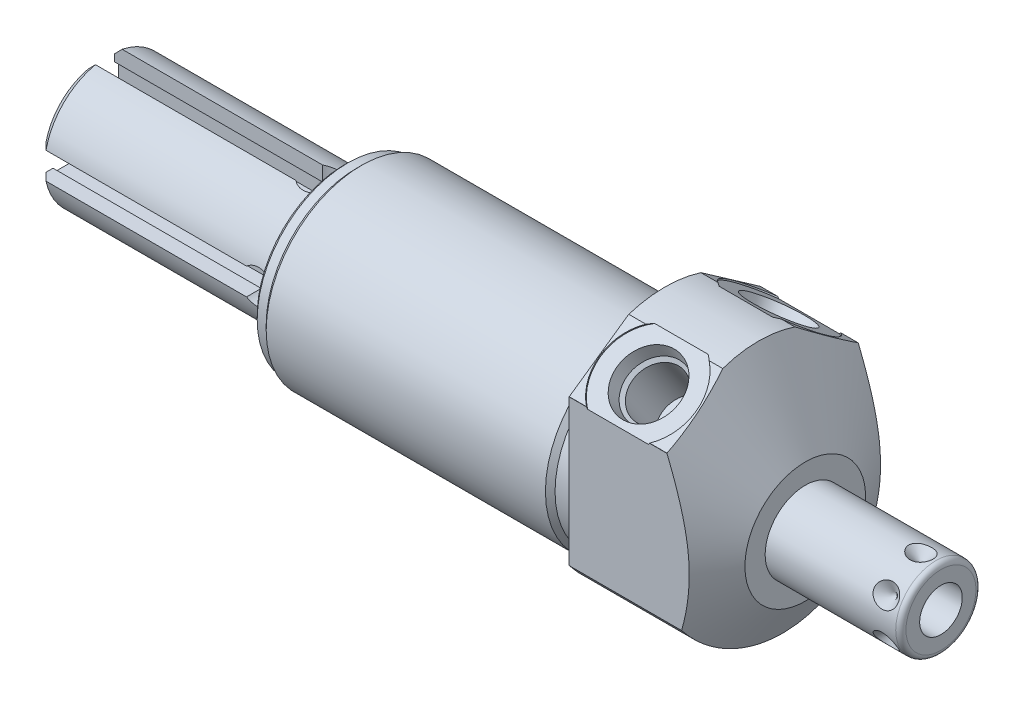
SolidWorks part; units mm, degrees
material "Alloy Steel"
ref_plane "Front Plane" through (0, 0, 0) normal (0, 0, 1) x (1, 0, 0)
ref_plane "Top Plane" through (0, 0, 0) normal (0, 1, 0) x (1, 0, 0)
ref_plane "Right Plane" through (0, 0, 0) normal (1, 0, 0) x (0, 0, -1)
ref_plane "Plane1" through (0, 0, 0) normal (1, 0, 0) x (0, 0, -1)
sketch "Sketch1" plane through (0, 0, 0) normal (1, 0, 0) x (0, 0, -1)
  circle A0 centre (0, 0) radius 23.8125
  dimension "D1" = 47.625
extrude "Extrude1" add sketch "Sketch1" along normal blind 27.7876 and the other way blind 63.5
ref_plane "Plane2" through (0, 0, 0) normal (1, 0, 0) x (0, 0, -1)
sketch "Sketch2" plane through (0, 0, 0) normal (1, 0, 0) x (0, 0, -1)
  line L0 (-20.7455, -4.191) -> (20.7455, -4.191) construction
  circle A0 centre (0, -4.191) radius 18.8595
  circle A1 centre (0, 0) radius 23.8125 construction
  circle A2 centre (0, 0) radius 23.8125
  dimension "D2" = 37.719
  dimension "D1" = 4.191
extrude "Cut-Extrude1" cut sketch "Sketch2" against normal up to next
ref_plane "Plane4" through (0, 0, 0) normal (-1, 0, 0) x (0, 0, 1)
sketch "Sketch4" plane through (0, 0, 0) normal (-1, 0, 0) x (0, 0, 1)
  line L0 (18.923, -14.4553) -> (18.923, 14.4659)
  line L1 (18.923, 14.4659) -> (0, 27.7159)
  line L2 (-18.923, -14.4553) -> (-18.923, 14.4659)
  line L3 (-18.923, 14.4659) -> (0, 27.7159)
  line L4 (0, -26.3889) -> (0, 30.2923) construction
  circle A0 centre (0, 0) radius 28.575
  circle A1 centre (0, 0) radius 23.8125 construction
  arc A3 (-18.923, -14.4553) -> (18.923, -14.4553) centre (0, 0) ccw
  dimension "D4" = 57.15
  dimension "D1" = 37.846
  dimension "D2" = 27.7159
  dimension "D3" = 55
extrude "Cut-Extrude3" cut sketch "Sketch4" against normal up to next
ref_plane "Plane6" through (0, 0, 0) normal (0, 0, 1) x (1, 0, 0)
sketch "Sketch6" plane through (0, 0, 0) normal (0, 0, 1) x (1, 0, 0)
  line L0 (4.764, 47.625) -> (27.7876, 7.747)
  line L1 (3.6128, -4.191) -> (28.9388, -4.191) construction
  line L2 (-63.5, -4.191) -> (0, -4.191) construction
  line L3 (27.7876, 7.747) -> (27.7876, 47.625)
  line L4 (27.7876, 47.625) -> (4.764, 47.625)
  line L5 (27.7876, -14.4553) -> (27.7876, 14.4553) construction
  dimension "D1" = 23.876
  dimension "D2" = 30
  dimension "D3" = 39.878
revolve "Cut-Revolve2" cut sketch "Sketch6" angle 360 about L1
ref_plane "Plane7" through (9.652, 18.3948, 12.869) normal (1, 0, 0) x (0, 0.5736, -0.8192)
sketch "S2D0002" plane through (9.652, 18.3948, 12.869) normal (1, 0, 0) x (0, 0.5736, -0.8192)
  line L0 (0, 0) -> (6.1849, 0)
  line L1 (6.1849, 0) -> (5.6423, -2.5527)
  line L2 (5.6423, -2.5527) -> (4.9784, -3.2166)
  line L3 (4.9784, -3.2166) -> (4.9784, -13.462)
  line L4 (4.9784, -13.462) -> (0, -13.462)
  line L5 (0, -13.462) -> (0, 0)
  line L6 (0, -14.1351) -> (0, 0.6731) construction
  dimension "D1" = 13.462
revolve "Cut-Revolve3" cut sketch "S2D0002" angle 360 about L6
ref_plane "Plane8" through (9.652, 18.3948, -12.869) normal (1, 0, 0) x (0, -0.5736, -0.8192)
sketch "Sketch8" plane through (9.652, 18.3948, -12.869) normal (1, 0, 0) x (0, -0.5736, -0.8192)
  line L0 (0, 0) -> (6.1849, 0)
  line L1 (6.1849, 0) -> (5.6423, -2.5527)
  line L2 (5.6423, -2.5527) -> (4.9784, -3.2166)
  line L3 (4.9784, -3.2166) -> (4.9784, -13.462)
  line L4 (4.9784, -13.462) -> (0, -13.462)
  line L5 (0, -13.462) -> (0, 0)
  line L6 (0, -14.1351) -> (0, 0.6731) construction
  dimension "D1" = 13.462
revolve "Cut-Revolve4" cut sketch "Sketch8" angle 360 about L6
sketch "Sketch18" plane through (0, 18.5976, 13.0222) normal (0, 0.8192, 0.5736) x (1, 0, 0)
  circle A0 centre (9.652, 0.0091) radius 9.525
  dimension "D1" = 19.05
extrude "Cut-Extrude4" cut sketch "Sketch18" against normal blind 0.254
sketch "Sketch19" plane through (0, 18.5976, -13.0222) normal (0, 0.8192, -0.5736) x (1, 0, 0)
  circle A0 centre (9.652, -0.0091) radius 9.525
  dimension "D1" = 19.05
extrude "Cut-Extrude5" cut sketch "Sketch19" against normal blind 0.254
ref_plane "Plane10" through (0, 0, 0) normal (0, 0, 1) x (1, 0, 0)
sketch "Sketch10" plane through (0, 0, 0) normal (0, 0, 1) x (1, 0, 0)
  line L0 (0, 14.6685) -> (0, 13.716)
  line L1 (0, 13.716) -> (-3.81, 13.716)
  line L2 (-3.81, 13.716) -> (-4.7625, 14.6685)
  line L3 (-5.0006, -4.191) -> (0.2381, -4.191) construction
  line L4 (0, 14.6685) -> (-4.7625, 14.6685)
  line L5 (-63.5, -4.191) -> (0, -4.191) construction
  line L6 (0, 14.6685) -> (-63.5, 14.6685) construction
  line L7 (0, 14.6685) -> (0, -23.0505) construction
  dimension "D1" = 35.814
  dimension "D2" = 3.81
  dimension "D3" = 45
revolve "Cut-Revolve6" cut sketch "Sketch10" angle 360 about L3
ref_plane "Plane12" through (0, 0, 0) normal (0, 0, 1) x (1, 0, 0)
sketch "Sketch12" plane through (0, 0, 0) normal (0, 0, 1) x (1, 0, 0)
  line L0 (-63.5, 14.6685) -> (-63.5, 13.716)
  line L1 (-63.5, 13.716) -> (-60.96, 13.716)
  line L2 (-60.96, 13.716) -> (-60.0075, 14.6685)
  line L3 (-63.6746, -4.191) -> (-59.8329, -4.191) construction
  line L4 (-63.5, 14.6685) -> (-60.0075, 14.6685)
  line L6 (-63.5, -4.191) -> (-4.7625, -4.191) construction
  line L7 (-4.7625, 14.6685) -> (-63.5, 14.6685) construction
  line L8 (-63.5, 14.6685) -> (-63.5, -23.0505) construction
  dimension "D1" = 35.814
  dimension "D2" = 2.54
  dimension "D3" = 45
revolve "Cut-Revolve8" cut sketch "Sketch12" angle 360 about L3
chamfer "Chamfer1" distance 0.762 angle 45 1 edges at (-63.5, -4.191, 17.907)
ref_plane "Plane13" through (0, 0, 0) normal (0, 0, 1) x (0, -1, 0)
sketch "Sketch13" plane through (0, 0, 0) normal (0, 0, 1) x (0, -1, 0)
  line L0 (4.191, 27.7876) -> (4.191, 54.6354)
  line L1 (4.191, 54.6354) -> (11.1125, 54.6354)
  line L2 (12.1285, 53.6194) -> (12.1285, 27.7876)
  line L3 (12.1285, 27.7876) -> (4.191, 27.7876)
  line L4 (4.191, 26.4452) -> (4.191, 55.9778) construction
  line L5 (4.191, -60.0075) -> (4.191, -4.7625) construction
  line L6 (16.129, 27.7876) -> (-7.747, 27.7876) construction
  line L7 (14.4553, 0) -> (-14.4553, 0) construction
  arc A0 (12.1285, 53.6194) -> (11.1125, 54.6354) centre (11.1125, 53.6194) ccw
  dimension "D2" = 1.016
  dimension "D1" = 54.6354
  dimension "D3" = 15.875
revolve "Revolve1" add sketch "Sketch13" angle 360 about L4
ref_plane "Plane14" through (54.6354, -8.4074, 0) normal (0, 0, 1) x (0, -1, 0)
sketch "S2D0001" plane through (54.6354, -8.4074, 0) normal (0, 0, 1) x (0, -1, 0)
  line L0 (0, 0) -> (0, -15.24)
  line L1 (0, -15.24) -> (-4.2164, -17.7735)
  line L2 (0, 0) -> (-4.2164, 0)
  line L3 (-4.2164, 0) -> (-4.2164, -17.7735)
  line L4 (-4.2164, -18.6621) -> (-4.2164, 0.8887) construction
  line L5 (-4.2164, -1.016) -> (-4.2164, -26.8478) construction
  line L6 (2.7051, 0) -> (-11.1379, 0) construction
  dimension "D1" = 8.4328
  dimension "D2" = 15.24
  dimension "D3" = 59
revolve "Cut-Revolve9" cut sketch "S2D0001" angle 360 about L4
ref_plane "Plane16" through (50.673, -12.1285, 0) normal (0, 0, 1) x (-1, 0, 0)
ref_plane "Plane17" through (0, -3.1433, -1.8148) normal (0, 0.866, 0.5) x (-1, 0, 0)
sketch "Sketch16" plane through (50.673, 3.7465, 0) normal (0, 0, -1) x (-1, 0, 0)
  line L0 (0, 0) -> (2.413, 0)
  line L1 (2.413, 0) -> (0, -2.413)
  line L2 (0, 0) -> (0, -2.413)
  line L3 (0, -5.071) -> (0, 0.1207) construction
  line L4 (-3.9624, -1.016) -> (-3.9624, -14.859) construction
  line L5 (22.8854, 0) -> (-2.9464, 0) construction
  dimension "D1" = 3.9624
  dimension "D2" = 4.826
  dimension "D3" = 45
revolve "Cut-Revolve10" cut sketch "Sketch16" angle 360 about L3
pattern_circular "CirPattern1" count 6 over 360 about axis through (26.4452, -4.191, 0) along (-1, 0, 0) of "Cut-Revolve10"
sketch "Sketch20" plane through (-63.5, 0, 0) normal (-1, 0, 0) x (0, 0, 1)
  circle A0 centre (0, -4.191) radius 12.7
  circle A1 centre (0, -4.191) radius 17.145 construction
  dimension "D1" = 25.4
extrude "Extrude2" add sketch "Sketch20" along normal blind 48.0314
chamfer "Chamfer2" distance 1.524 angle 45 1 edges at (-111.5314, -4.191, 12.7)
sketch "Sketch21" plane through (-63.5, 0, 0) normal (-1, 0, 0) x (0, 0, 1)
  circle A0 centre (0, -4.191) radius 12.7 construction
  circle A1 centre (0, -4.191) radius 12.7
  circle A2 centre (0, -4.191) radius 16.129
  dimension "D1" = 32.258
extrude "Cut-Extrude6" cut sketch "Sketch21" against normal blind 0.127
sketch "Sketch22" plane through (-63.373, 0, 0) normal (-1, 0, 0) x (0, 0, 1)
  circle A0 centre (0, -4.191) radius 16.129 construction
  circle A1 centre (0, -4.191) radius 16.129
  circle A2 centre (0, -4.191) radius 15.875
  dimension "D1" = 31.75
extrude "Cut-Extrude7" cut sketch "Sketch22" against normal blind 1.397
sketch "Sketch23" plane through (-111.5314, 0, 0) normal (-1, 0, 0) x (0, 0, 1)
  line L0 (0, -4.191) -> (-13.9301, -4.191) construction
  line L1 (-12.4222, -6.8326) -> (-9.5123, -6.8326)
  line L2 (-9.5123, -6.8326) -> (-9.5123, -7.62)
  line L3 (-9.5123, -7.62) -> (-6.2103, -7.62)
  line L4 (-6.2103, -7.62) -> (-6.2103, -0.762)
  line L5 (-9.5123, -0.762) -> (-6.2103, -0.762)
  line L6 (-12.4222, -1.5494) -> (-9.5123, -1.5494)
  line L7 (-9.5123, -1.5494) -> (-9.5123, -0.762)
  circle A1 centre (0, -4.191) radius 12.7 construction
  arc A2 (-12.4222, -1.5494) -> (-12.4222, -6.8326) centre (0, -4.191) ccw
  dimension "D3" = 3.302
  dimension "D4" = 6.4897
  dimension "D1" = 5.2832
  dimension "D2" = 6.858
extrude "Cut-Extrude8" cut sketch "Sketch23" against normal offset from surface (43.3832 mm away) 4.7752 up to face at (-63.373, -4.191, 12.7)
sketch "Sketch24" plane through (0, 0, -6.2103) normal (0, 0, -1) x (1, 0, 0)
  line L0 (-68.1482, 7.62) -> (-68.1482, 0.762) construction
  line L1 (-63.5, 21.336) -> (-63.5, -12.954) construction
  circle A0 centre (-68.1482, 4.191) radius 3.429
  dimension "D1" = 6.858
  dimension "D2" = 4.6482
extrude "Cut-Extrude9" cut sketch "Sketch24" along normal through all
pattern_circular "CirPattern2" count 4 over 360 about axis through (0, -4.191, 0) along (1, 0, 0) of "Cut-Extrude8", "Cut-Extrude9"
